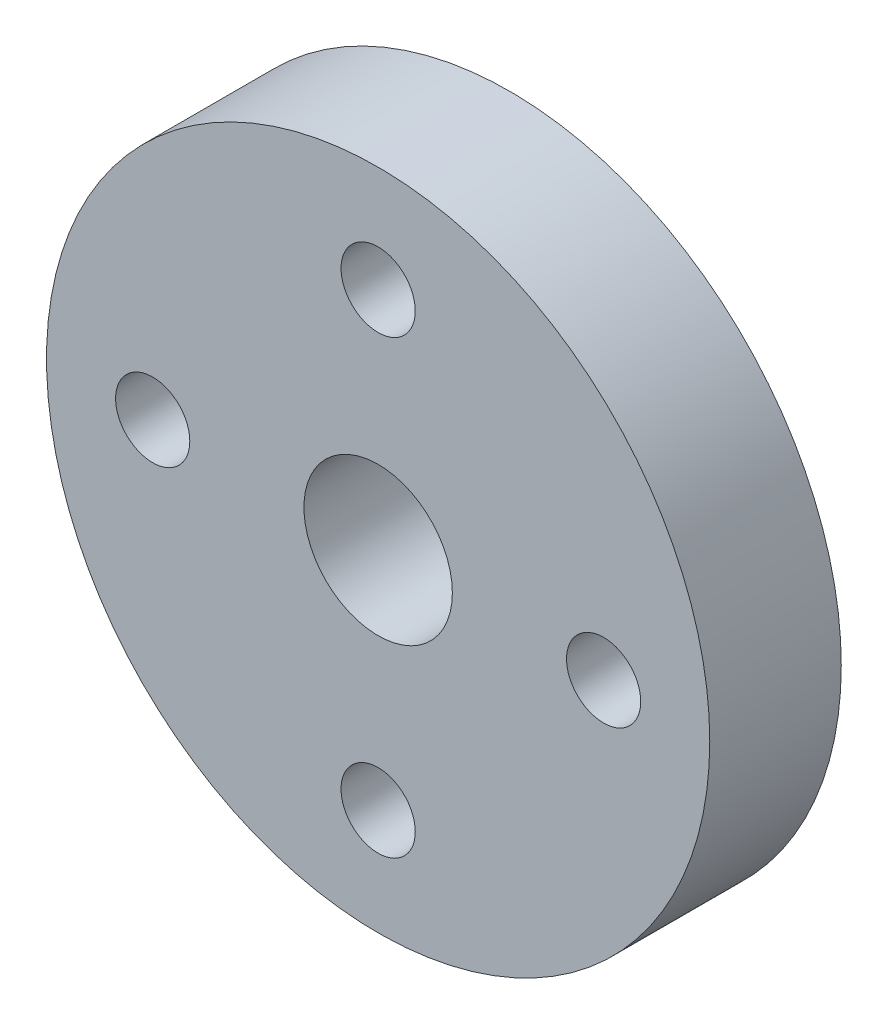
SolidWorks part; units mm, degrees
ref_plane "Front Plane" through (0, 0, 0) normal (0, 0, 1) x (1, 0, 0)
ref_plane "Top Plane" through (0, 0, 0) normal (0, 1, 0) x (1, 0, 0)
ref_plane "Right Plane" through (0, 0, 0) normal (1, 0, 0) x (0, 0, -1)
sketch "Sketch1" plane through (0, 0, 0) normal (0, 0, 1) x (1, 0, 0)
  line L0 (0, 0) -> (0, 17.65) construction
  line L1 (0, 0) -> (-17.65, 0) construction
  circle A0 centre (0, 0) radius 17.65
  circle A1 centre (0, 0) radius 3.95
  circle A2 centre (0, 12) radius 1.975
  circle A3 centre (12, 0) radius 1.975
  circle A4 centre (0, -12) radius 1.975
  circle A5 centre (-12, 0) radius 1.975
  point P17 (0, 0)
  dimension "D1" = 35.3
  dimension "D2" = 7.9
  dimension "D3" = 3.95
  dimension "D4" = 12
  dimension "D5" = 4
extrude "Boss-Extrude1" add sketch "Sketch1" along normal blind 7
